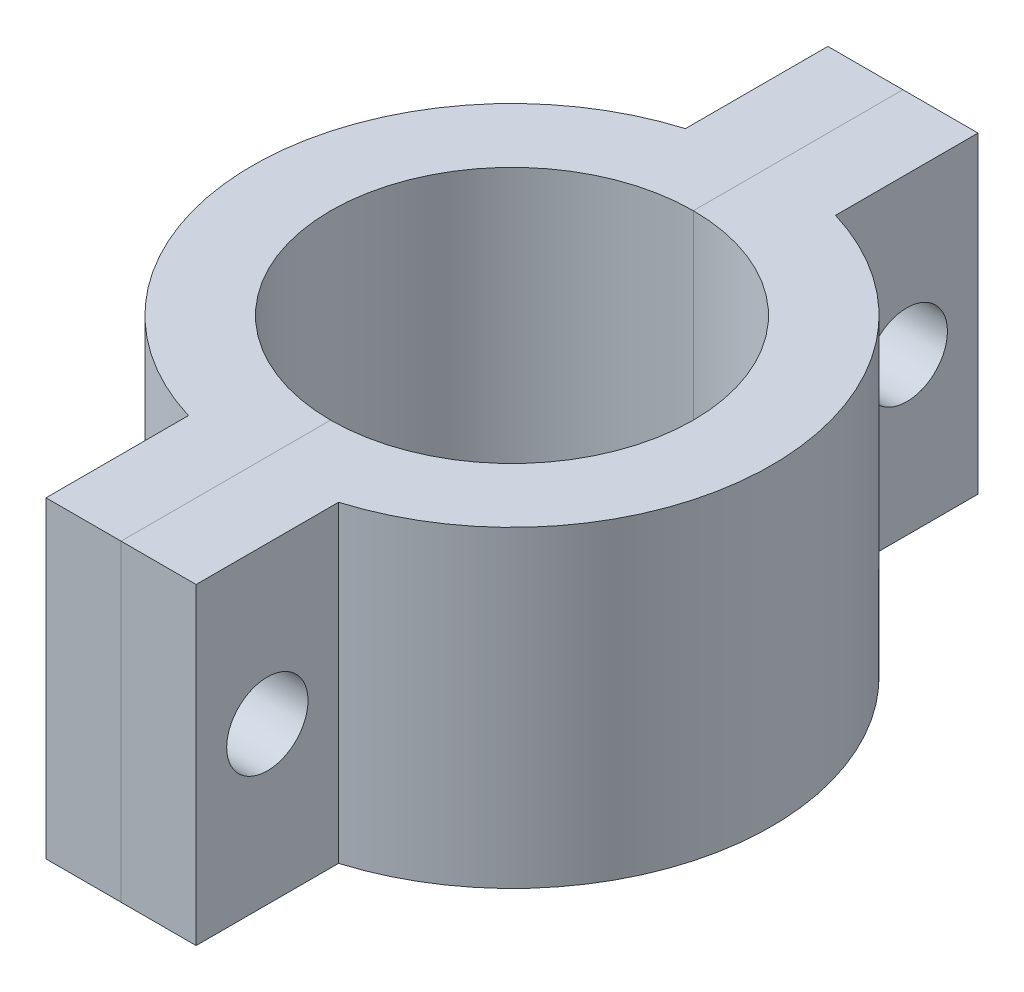
SolidWorks part; units mm, degrees
ref_plane "Front Plane" through (0, 0, 0) normal (0, 0, 1) x (1, 0, 0)
ref_plane "Top Plane" through (0, 0, 0) normal (0, 1, 0) x (1, 0, 0)
ref_plane "Right Plane" through (0, 0, 0) normal (1, 0, 0) x (0, 0, -1)
sketch "Sketch1" plane through (0, 0, 0) normal (0, 1, 0) x (1, 0, 0)
  line L5 (-6.096, 31.75) -> (6.096, 31.75)
  line L6 (-6.096, 31.75) -> (-6.096, -31.75)
  line L7 (-6.096, -31.75) -> (6.096, -31.75)
  line L8 (6.096, 31.75) -> (6.096, -31.75)
  line L9 (-6.096, 31.75) -> (6.096, -31.75) construction
  line L10 (-6.096, -31.75) -> (6.096, 31.75) construction
  circle A0 centre (0, 0) radius 14.732
  circle A1 centre (0, 0) radius 21.082
  dimension "D1" = 29.464
  dimension "D2" = 6.35
  dimension "D3" = 63.5
  dimension "D4" = 12.192
extrude "Boss-Extrude2" add sketch "Sketch1" along normal blind 25.4 contours L6 A1 A0 | A1 L6 L7 L8 | L8 A1 A0 | L6 A1 L8 A0 | L8 A1 L6 A0 | A1 L8 L5 L6
sketch "Sketch2" plane through (-6.096, 0, 0) normal (-1, 0, 0) x (0, 0, 1)
  line L0 (31.75, 25.4) -> (31.75, 0) construction
  line L1 (20.1814, 25.4) -> (31.75, 25.4) construction
  line L2 (-31.75, 25.4) -> (-20.1814, 25.4) construction
  circle A0 centre (-25.9657, 12.7) radius 3.302
  circle A1 centre (25.9657, 12.7) radius 3.302
  point P6 (31.75, 12.7)
  point P9 (25.9657, 25.4)
  point P12 (-25.9657, 25.4)
  dimension "D1" = 6.604
  dimension "D2" = 6.604
extrude "Cut-Extrude1" cut sketch "Sketch2" against normal up to next
sketch "Sketch3" plane through (-6.096, 0, 0) normal (-1, 0, 0) x (0, 0, 1)
  circle A0 centre (-25.9657, 12.7) radius 4.7625
  circle A1 centre (25.9657, 12.7) radius 4.7625
  dimension "D1" = 9.525
extrude "Cut-Extrude2" cut sketch "Sketch3" against normal blind 5.08
ref_plane "Plane1" through (0, 0, 0) normal (-1, 0, 0) x (0, 0, 1)
split "Split1" trim tools "Plane1" bodies to split 104 resulting bodies 105 106
